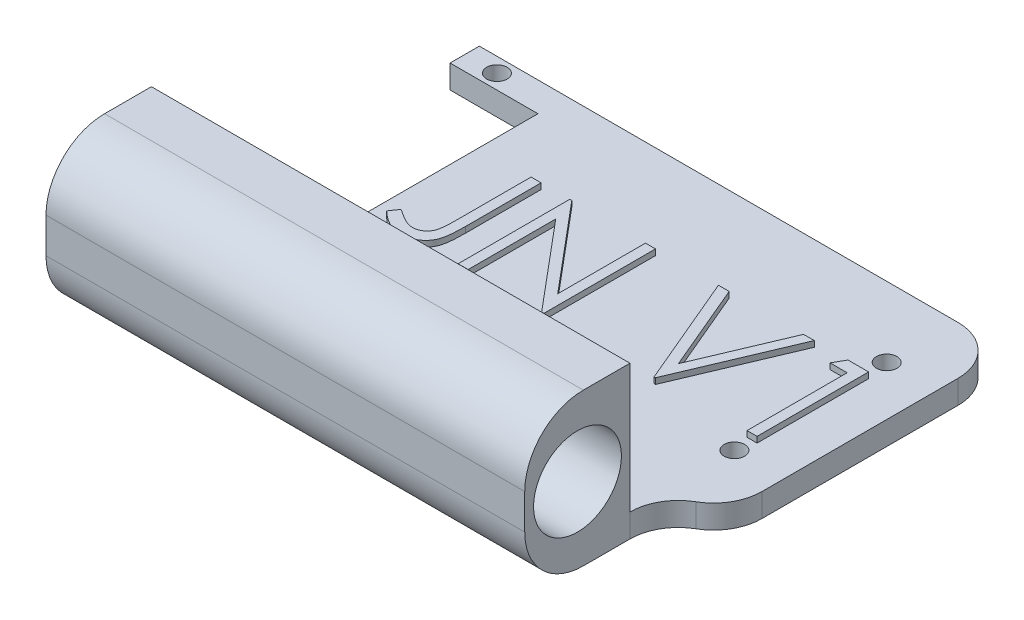
SolidWorks part; units mm, degrees
ref_plane "Front Plane" through (0, 0, 0) normal (0, 0, 1) x (1, 0, 0)
ref_plane "Top Plane" through (0, 0, 0) normal (0, 1, 0) x (1, 0, 0)
ref_plane "Right Plane" through (0, 0, 0) normal (1, 0, 0) x (0, 0, -1)
sketch "Sketch1" plane through (0, 0, 0) normal (0, 1, 0) x (1, 0, 0)
  line L0 (0, 45) -> (15, 45)
  line L1 (0, 0) -> (90, 0)
  line L3 (0, 50) -> (90, 50)
  line L4 (90, 0) -> (90, 50)
  line L5 (15, 45) -> (15, 5)
  line L6 (0, 5) -> (15, 5)
  line L7 (0, 45) -> (0, 50)
  line L8 (0, 5) -> (0, 0)
  circle A0 centre (5.5, 2.5) radius 1.75
  circle A1 centre (5.5, 47.5) radius 1.75
  circle A2 centre (81.55, 12) radius 1.75
  circle A3 centre (81.55, 38) radius 1.75
  dimension "D3" = 2.5
  dimension "D7" = 12
  dimension "D9" = 12
  dimension "D1" = 50
  dimension "D2" = 90
  dimension "D6" = 2.5
  dimension "D8" = 8.45
  dimension "D10" = 8.45
  dimension "D11" = 15
  dimension "D12" = 15
extrude "Boss-Extrude1" add sketch "Sketch1" along normal blind 4
fillet "Fillet1" radius 8.25 2 edges at (90, 2, -50) (90, 2, 0)
sketch "Sketch2" plane through (0, 0, 0) normal (0, 0, 1) x (1, 0, 0)
  line L1 (0, 4) -> (81.75, 4)
  line L2 (0, 4) -> (0, 0)
  line L3 (0, 0) -> (81.75, 0)
  line L4 (81.75, 4) -> (81.75, 0)
extrude "Boss-Extrude2" add sketch "Sketch2" along normal blind 24
sketch "Sketch3" plane through (0, 0, 0) normal (0, -1, 0) x (1, 0, 0)
  line L1 (81.75, 0) -> (0, 0)
  line L2 (81.75, 0) -> (81.75, 24)
  line L3 (81.75, 24) -> (0, 24)
  line L4 (0, 0) -> (0, 24)
sketch "Sketch4" plane through (81.75, 0, 0) normal (1, 0, 0) x (0, 0, -1)
  circle A0 centre (-9, -9) radius 7.5
fillet "Fillet3" radius 8.25 1 edges at (81.75, 2, 0)
sketch "Sketch5" plane through (0, 4, 0) normal (0, 1, 0) x (1, 0, 0)
  text T0 "JN V1</r>" font "Century Gothic" height in points 72
extrude "Boss-Extrude4" add sketch "Sketch5" along normal blind 1
sketch "Sketch6" plane through (0, 4, 0) normal (0, 1, 0) x (1, 0, 0)
  line L0 (0, -24) -> (0, -6)
  line L3 (0, -24) -> (81.75, -24)
  line L5 (0, 0) -> (0, -24) construction
  line L6 (0, -6) -> (81.75, -6.0394)
  line L7 (81.75, -6.0394) -> (81.75, -24)
extrude "Boss-Extrude6" add sketch "Sketch6" along normal blind 22
sketch "Sketch7" plane through (0, 0, 0) normal (-1, 0, 0) x (0, 0, 1)
  circle A0 centre (15, 13) radius 7.5
  point P2 (15, 13)
extrude "Cut-Extrude2" cut sketch "Sketch7" against normal blind 115
fillet "Fillet6" radius 10 2 edges at (40.875, 0, 24) (40.875, 26, 24)
